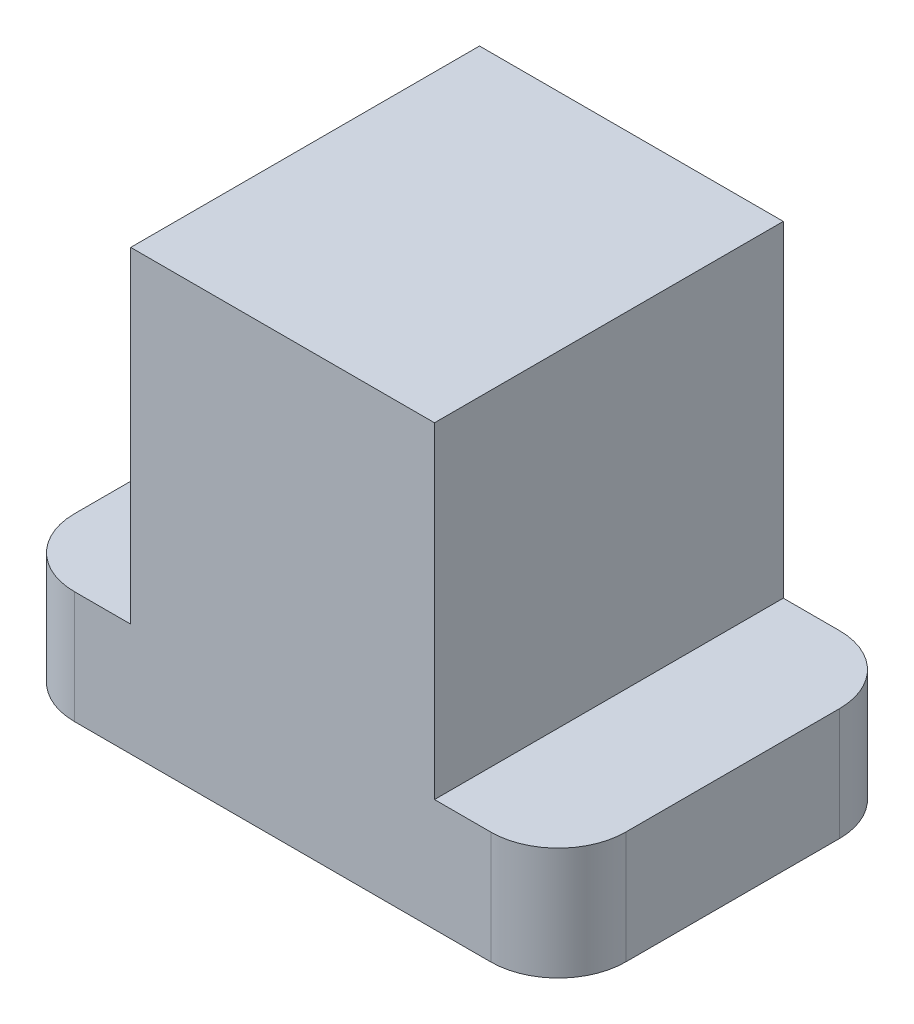
SolidWorks part; units mm, degrees
ref_plane "Спереди" through (0, 0, 0) normal (0, 0, 1) x (1, 0, 0)
ref_plane "Сверху" through (0, 0, 0) normal (0, 1, 0) x (1, 0, 0)
ref_plane "Справа" through (0, 0, 0) normal (1, 0, 0) x (0, 0, -1)
other "Configuration Table"
sketch "Эскиз2" plane through (0, 0, 0) normal (0, 1, 0) x (1, 0, 0)
  line L1 (-37, -31) -> (37, -31)
  line L2 (-49, -19) -> (-49, 19)
  line L3 (-37, 31) -> (37, 31)
  line L4 (49, -19) -> (49, 19)
  line L5 (-49, -31) -> (49, 31) construction
  line L6 (-49, 31) -> (49, -31) construction
  arc A0 (37, 31) -> (49, 19) centre (37, 19) cw
  arc A1 (37, -31) -> (49, -19) centre (37, -19) ccw
  arc A2 (-37, -31) -> (-49, -19) centre (-37, -19) cw
  arc A3 (-49, 19) -> (-37, 31) centre (-37, 19) cw
  point P0 (0, 0)
  dimension "D3" = 12
  dimension "D1" = 62
  dimension "D2" = 98
extrude "Бобышка-Вытянуть1" add sketch "Эскиз2" along normal blind 20
sketch "Эскиз3" plane through (0, 20, 0) normal (0, 1, 0) x (1, 0, 0)
  line L1 (-27, -31) -> (27, -31)
  line L2 (-27, -31) -> (-27, 31)
  line L3 (-27, 31) -> (27, 31)
  line L4 (27, -31) -> (27, 31)
  line L5 (-27, -31) -> (27, 31) construction
  line L6 (-27, 31) -> (27, -31) construction
  point P0 (0, 0)
  dimension "D1" = 62
  dimension "D2" = 54
extrude "Бобышка-Вытянуть2" add sketch "Эскиз3" along normal blind 58
